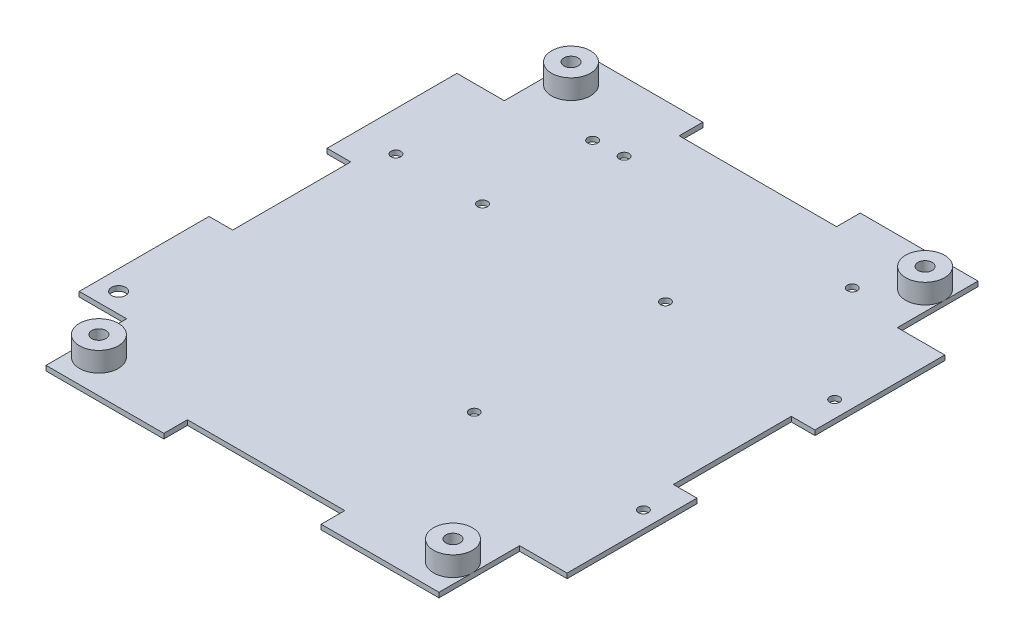
SolidWorks part; units mm, degrees
ref_plane "Front Plane" through (0, 0, 0) normal (0, 0, 1) x (1, 0, 0)
ref_plane "Top Plane" through (0, 0, 0) normal (0, 1, 0) x (1, 0, 0)
ref_plane "Right Plane" through (0, 0, 0) normal (1, 0, 0) x (0, 0, -1)
sketch "Sketch1" plane through (0, 0, 0) normal (0, 1, 0) x (1, 0, 0)
  line L0 (-25.4, 86.995) -> (-63.4314, 86.995)
  line L1 (-88.9, -101.6) -> (88.9, -101.6) construction
  line L2 (101.6, -88.9) -> (101.6, 88.9) construction
  line L3 (88.9, 101.6) -> (-88.9, 101.6) construction
  line L4 (-78.74, -60.96) -> (-63.4314, -60.96)
  line L5 (-63.4314, -60.96) -> (-63.4314, -86.995)
  line L6 (-63.4314, -86.995) -> (-25.4, -86.995)
  line L7 (63.4314, -86.995) -> (63.4314, -60.96)
  line L8 (63.4314, -60.96) -> (78.74, -60.96)
  line L9 (78.74, -60.96) -> (78.74, -25.4)
  line L10 (78.74, 60.96) -> (63.4314, 60.96)
  line L11 (63.4314, 60.96) -> (63.4314, 86.995)
  line L12 (63.4314, 86.995) -> (25.4, 86.995)
  line L13 (-63.4314, 86.995) -> (-63.4314, 60.96)
  line L14 (-63.4314, 60.96) -> (-78.74, 60.96)
  line L15 (-78.74, 60.96) -> (-78.74, 25.4)
  line L16 (-78.74, -25.4) -> (-78.74, -60.96)
  line L17 (-78.74, -25.4) -> (-71.12, -25.4)
  line L19 (-78.74, 25.4) -> (-71.12, 25.4)
  line L20 (-71.12, -25.4) -> (-71.12, 25.4)
  line L22 (-25.4, 86.995) -> (-25.4, 79.375)
  line L23 (-25.4, 79.375) -> (25.4, 79.375)
  line L24 (25.4, 86.995) -> (25.4, 79.375)
  line L25 (78.74, 25.4) -> (71.12, 25.4)
  line L27 (78.74, -25.4) -> (71.12, -25.4)
  line L28 (71.12, 25.4) -> (71.12, -25.4)
  line L30 (25.4, -86.995) -> (25.4, -79.375)
  line L31 (25.4, -79.375) -> (-25.4, -79.375)
  line L32 (-25.4, -86.995) -> (-25.4, -79.375)
  line L33 (78.74, 25.4) -> (78.74, 60.96)
  line L34 (25.4, -86.995) -> (63.4314, -86.995)
  line L35 (-101.6, 88.9) -> (-101.6, -88.9) construction
  arc A0 (88.9, -101.6) -> (101.6, -88.9) centre (88.9, -88.9) ccw construction
  arc A1 (-101.6, -88.9) -> (-88.9, -101.6) centre (-88.9, -88.9) ccw construction
  arc A2 (101.6, 88.9) -> (88.9, 101.6) centre (88.9, 88.9) ccw construction
  arc A3 (-101.6, 88.9) -> (-88.9, 101.6) centre (-88.9, 88.9) cw construction
  circle A4 centre (-57.15, 76.2) radius 2.286
  circle A5 centre (57.15, 76.2) radius 2.286
  circle A6 centre (57.15, -76.2) radius 2.286
  circle A7 centre (-57.15, -76.2) radius 2.286
  point P3 (0, 101.6)
  point P5 (101.6, 0)
  point P13 (101.6, 101.6)
  point P16 (-101.6, 101.6)
  point P38 (-71.12, 0)
  point P55 (0, -79.375)
  point P56 (0, 79.375)
  point P57 (71.12, 0)
  dimension "D2" = 12.7
  dimension "D11" = 4.572
  dimension "D8" = 44.45
  dimension "D1" = 203.2
  dimension "D3" = 203.2
  dimension "D4" = 22.86
  dimension "D5" = 15.3086
  dimension "D6" = 35.56
  dimension "D7" = 173.99
  dimension "D12" = 50.8
  dimension "D13" = 25.4
  dimension "D14" = 44.45
  dimension "D15" = 25.4
  dimension "D18" = 7.62
extrude "Main Body" add sketch "Sketch1" along normal blind 1.5875
sketch "Sketch5" plane through (0, 1.5875, 0) normal (0, 1, 0) x (1, 0, 0)
  line L0 (73.406, 30.734) -> (18.796, 30.734)
  line L1 (48.895, 90.17) -> (-32.385, 90.17)
  line L2 (48.895, 90.17) -> (48.895, 39.37)
  line L3 (48.895, 39.37) -> (-32.385, 39.37)
  line L4 (-32.385, 90.17) -> (-32.385, 39.37)
  line L5 (48.895, 90.17) -> (-32.385, 39.37) construction
  line L6 (48.895, 39.37) -> (-32.385, 90.17) construction
  line L7 (45.085, 64.77) -> (-28.575, 64.77)
  line L8 (-60.96, -54.61) -> (-15.24, -54.61)
  line L9 (-60.96, -54.61) -> (-60.96, 11.43)
  line L10 (-60.96, 11.43) -> (-15.24, 11.43)
  line L11 (-15.24, -54.61) -> (-15.24, 11.43)
  line L13 (-35.56, 26.035) -> (-68.58, 26.035)
  line L14 (-35.56, 26.035) -> (-35.56, 66.675)
  line L15 (-35.56, 66.675) -> (-68.58, 66.675)
  line L16 (-68.58, 26.035) -> (-68.58, 66.675)
  line L17 (-35.56, 26.035) -> (-68.58, 66.675) construction
  line L18 (-35.56, 66.675) -> (-68.58, 26.035) construction
  line L19 (-38.1, 28.575) -> (-66.04, 28.575)
  line L20 (-38.1, 28.575) -> (-38.1, 64.135)
  line L21 (-38.1, 64.135) -> (-66.04, 64.135)
  line L22 (-66.04, 28.575) -> (-66.04, 64.135)
  line L23 (-38.1, 28.575) -> (-66.04, 64.135) construction
  line L24 (-38.1, 64.135) -> (-66.04, 28.575) construction
  line L26 (73.406, -30.988) -> (18.796, -30.988)
  line L28 (73.406, -30.988) -> (73.406, 30.734)
  line L30 (73.406, 30.734) -> (18.796, 30.734)
  line L31 (18.796, -30.988) -> (18.796, 30.734)
  line L32 (73.406, -30.988) -> (18.796, 30.734) construction
  line L33 (73.406, 30.734) -> (18.796, -30.988) construction
  line L36 (25.4, 86.995) -> (25.4, 79.375)
  line L38 (25.4, 79.375) -> (-25.4, 79.375)
  line L40 (71.12, 25.4) -> (78.74, 25.4)
  line L41 (78.74, 25.4) -> (78.74, 60.96)
  line L42 (78.74, 60.96) -> (63.4314, 60.96)
  line L43 (63.4314, 60.96) -> (63.4314, 86.995)
  line L44 (63.4314, 86.995) -> (25.4, 86.995)
  line L45 (25.4, 79.375) -> (-25.4, 79.375)
  line L49 (-63.4314, 86.995) -> (-63.4314, 60.96)
  line L50 (-63.4314, 60.96) -> (-78.74, 60.96)
  line L51 (-78.74, 60.96) -> (-78.74, 25.4)
  line L52 (-78.74, 25.4) -> (-71.12, 25.4)
  line L53 (-71.12, 25.4) -> (-71.12, -25.4)
  line L54 (-71.12, -25.4) -> (-78.74, -25.4)
  line L55 (-78.74, -25.4) -> (-78.74, -60.96)
  line L56 (-78.74, -60.96) -> (-63.4314, -60.96)
  line L57 (-63.4314, -60.96) -> (-63.4314, -86.995)
  line L58 (-63.4314, -86.995) -> (-25.4, -86.995)
  line L61 (71.12, -25.4) -> (71.12, 25.4)
  line L62 (71.12, -25.4) -> (71.12, 25.4)
  line L63 (63.4314, -86.995) -> (63.4314, -60.96)
  line L64 (63.4314, -60.96) -> (78.74, -60.96)
  line L65 (78.74, -60.96) -> (78.74, -25.4)
  line L66 (78.74, -25.4) -> (71.12, -25.4)
  line L74 (71.12, 25.4) -> (78.74, 25.4)
  line L75 (78.74, 25.4) -> (78.74, 60.96)
  line L76 (78.74, 60.96) -> (63.4314, 60.96)
  line L77 (63.4314, 60.96) -> (63.4314, 86.995)
  line L78 (63.4314, 86.995) -> (25.4, 86.995)
  line L83 (-63.4314, 86.995) -> (-63.4314, 60.96)
  line L84 (-63.4314, 60.96) -> (-78.74, 60.96)
  line L85 (-78.74, 60.96) -> (-78.74, 25.4)
  line L86 (-78.74, 25.4) -> (-71.12, 25.4)
  line L87 (-71.12, 25.4) -> (-71.12, -25.4)
  line L88 (-71.12, -25.4) -> (-78.74, -25.4)
  line L89 (-78.74, -25.4) -> (-78.74, -60.96)
  line L90 (-78.74, -60.96) -> (-63.4314, -60.96)
  line L91 (-63.4314, -60.96) -> (-63.4314, -86.995)
  line L92 (-63.4314, -86.995) -> (-25.4, -86.995)
  line L97 (63.4314, -86.995) -> (63.4314, -60.96)
  line L98 (63.4314, -60.96) -> (78.74, -60.96)
  line L99 (78.74, -60.96) -> (78.74, -25.4)
  line L100 (78.74, -25.4) -> (71.12, -25.4)
  line L107 (-25.4, 86.995) -> (-63.4314, 86.995)
  line L109 (-25.4, 86.995) -> (-63.4314, 86.995)
  line L110 (-25.4, -86.995) -> (-25.4, -79.375)
  line L111 (-25.4, -86.995) -> (-25.4, -79.375)
  line L112 (-25.4, -79.375) -> (25.4, -79.375)
  line L113 (-25.4, -79.375) -> (25.4, -79.375)
  line L114 (25.4, -79.375) -> (25.4, -86.995)
  line L115 (25.4, -79.375) -> (25.4, -86.995)
  line L116 (25.4, -86.995) -> (63.4314, -86.995)
  line L117 (25.4, -86.995) -> (63.4314, -86.995)
  line L122 (25.4, 86.995) -> (25.4, 79.375)
  line L126 (-25.4, 79.375) -> (-25.4, 86.995)
  line L127 (-25.4, 79.375) -> (-25.4, 86.995)
  circle A0 centre (18.796, 30.734) radius 1.5875
  circle A1 centre (73.406, 30.734) radius 1.5875
  circle A2 centre (73.406, -30.988) radius 1.5875
  circle A3 centre (18.796, -30.988) radius 1.5875
  circle A4 centre (-15.24, -54.61) radius 1.27
  circle A5 centre (-60.96, -54.61) radius 1.27
  circle A6 centre (-60.96, 11.43) radius 1.27
  circle A7 centre (-15.24, 11.43) radius 1.27
  circle A8 centre (-28.575, 64.77) radius 1.5875
  circle A9 centre (45.085, 64.77) radius 1.5875
  circle A10 centre (-66.04, 28.575) radius 1.5875
  circle A11 centre (-66.04, 64.135) radius 1.5875
  circle A12 centre (-38.1, 64.135) radius 1.5875
  circle A13 centre (-38.1, 28.575) radius 1.5875
  circle A14 centre (57.15, 76.2) radius 2.286 construction
  circle A15 centre (-57.15, 76.2) radius 2.286 construction
  circle A16 centre (57.15, 76.2) radius 2.286
  circle A17 centre (-57.15, 76.2) radius 2.286
  circle A18 centre (57.15, 76.2) radius 6.2814
  circle A19 centre (-57.15, 76.2) radius 6.2814
  circle A20 centre (-72.39, -54.61) radius 2.286
  text T0 "<b>LIPO</b>"
  point P0 (8.255, 64.77)
  point P2 (73.406, -30.988)
  point P4 (18.796, -30.988)
  point P6 (18.796, 30.734)
  point P8 (73.406, 30.734)
  point P25 (46.101, 30.734)
  point P40 (-15.24, -21.59)
  point P42 (-38.1, 11.43)
  point P44 (-38.1, -21.59)
  point P52 (-52.07, 46.355)
  point P57 (-52.07, 46.355)
  point P58 (8.255, 64.77)
  point P78 (-52.07, 66.675)
  point P81 (46.101, -0.127)
  dimension "D8" = 3.175
  dimension "D9" = 3.175
  dimension "D10" = 3.175
  dimension "D11" = 3.175
  dimension "D17" = 2.54
  dimension "D20" = 3.175
  dimension "D27" = 3.175
  dimension "D30" = 4.572
  dimension "D33" = 5.334
  dimension "D14" = 5.334
  dimension "D2" = 54.61
  dimension "D4" = 81.28
  dimension "D5" = 61.722
  dimension "D6" = 50.8
  dimension "D7" = 22.225
  dimension "D12" = 21.59
  dimension "D13" = 28.575
  dimension "D15" = 45.72
  dimension "D16" = 66.04
  dimension "D18" = 21.59
  dimension "D19" = 38.1
  dimension "D21" = 73.66
  dimension "D22" = 3.175
  dimension "D23" = 40.64
  dimension "D24" = 33.02
  dimension "D25" = 35.56
  dimension "D26" = 27.94
  dimension "D28" = 3.175
  dimension "D29" = 9.525
  dimension "D31" = 6.35
  dimension "D32" = 6.35
  dimension "D1" = 0
sketch "Sketch13" plane through (0, 1.5875, 0) normal (0, 1, 0) x (1, 0, 0)
  line L32 (25.4, 79.375) -> (-25.4, 79.375)
  line L33 (25.4, 86.995) -> (25.4, 79.375)
  line L36 (63.4314, 86.995) -> (25.4, 86.995)
  line L37 (-63.4314, 86.995) -> (-63.4314, 60.96)
  line L38 (-63.4314, 60.96) -> (-78.74, 60.96)
  line L39 (-78.74, 60.96) -> (-78.74, 25.4)
  line L40 (-78.74, 25.4) -> (-71.12, 25.4)
  line L41 (-71.12, 25.4) -> (-71.12, -25.4)
  line L42 (-71.12, -25.4) -> (-78.74, -25.4)
  line L43 (-78.74, -25.4) -> (-78.74, -60.96)
  line L44 (-78.74, -60.96) -> (-63.4314, -60.96)
  line L45 (-63.4314, -60.96) -> (-63.4314, -86.995)
  line L46 (-63.4314, -86.995) -> (-25.4, -86.995)
  line L47 (-25.4, -86.995) -> (-25.4, -79.375)
  line L48 (-25.4, -79.375) -> (25.4, -79.375)
  line L49 (25.4, -79.375) -> (25.4, -86.995)
  line L50 (25.4, -86.995) -> (63.4314, -86.995)
  line L51 (63.4314, -86.995) -> (63.4314, -60.96)
  line L52 (63.4314, -60.96) -> (78.74, -60.96)
  line L53 (78.74, -60.96) -> (78.74, -25.4)
  line L54 (78.74, -25.4) -> (71.12, -25.4)
  line L55 (71.12, -25.4) -> (71.12, 25.4)
  line L56 (71.12, 25.4) -> (78.74, 25.4)
  line L57 (78.74, 25.4) -> (78.74, 60.96)
  line L58 (78.74, 60.96) -> (63.4314, 60.96)
  line L59 (63.4314, 60.96) -> (63.4314, 86.995)
  line L60 (-25.4, 86.995) -> (-63.4314, 86.995)
  line L61 (25.4, 86.995) -> (25.4, 79.375)
  line L64 (25.4, 79.375) -> (-25.4, 79.375)
  line L68 (63.4314, 86.995) -> (25.4, 86.995)
  line L69 (-63.4314, 86.995) -> (-63.4314, 60.96)
  line L70 (-63.4314, 60.96) -> (-78.74, 60.96)
  line L71 (-78.74, 60.96) -> (-78.74, 25.4)
  line L72 (-78.74, 25.4) -> (-71.12, 25.4)
  line L73 (-71.12, 25.4) -> (-71.12, -25.4)
  line L74 (-71.12, -25.4) -> (-78.74, -25.4)
  line L75 (-78.74, -25.4) -> (-78.74, -60.96)
  line L76 (-78.74, -60.96) -> (-63.4314, -60.96)
  line L77 (-63.4314, -60.96) -> (-63.4314, -86.995)
  line L78 (-63.4314, -86.995) -> (-25.4, -86.995)
  line L79 (-25.4, -86.995) -> (-25.4, -79.375)
  line L80 (-25.4, -79.375) -> (25.4, -79.375)
  line L81 (25.4, -79.375) -> (25.4, -86.995)
  line L82 (25.4, -86.995) -> (63.4314, -86.995)
  line L83 (63.4314, -86.995) -> (63.4314, -60.96)
  line L84 (63.4314, -60.96) -> (78.74, -60.96)
  line L85 (78.74, -60.96) -> (78.74, -25.4)
  line L86 (78.74, -25.4) -> (71.12, -25.4)
  line L87 (71.12, -25.4) -> (71.12, 25.4)
  line L88 (71.12, 25.4) -> (78.74, 25.4)
  line L89 (78.74, 25.4) -> (78.74, 60.96)
  line L90 (78.74, 60.96) -> (63.4314, 60.96)
  line L91 (63.4314, 60.96) -> (63.4314, 86.995)
  line L104 (-25.4, 79.375) -> (-25.4, 86.995)
  line L105 (-25.4, 79.375) -> (-25.4, 86.995)
  line L108 (-25.4, 86.995) -> (-63.4314, 86.995)
  circle A0 centre (57.15, 76.2) radius 2.286 construction
  circle A1 centre (-57.15, 76.2) radius 2.286 construction
  circle A2 centre (-57.15, -76.2) radius 2.286 construction
  circle A3 centre (57.15, -76.2) radius 2.286 construction
  circle A4 centre (57.15, 76.2) radius 2.286
  circle A5 centre (-57.15, 76.2) radius 2.286
  circle A6 centre (-57.15, -76.2) radius 2.286
  circle A7 centre (57.15, -76.2) radius 2.286
  circle A8 centre (57.15, 76.2) radius 6.2814
  circle A9 centre (-57.15, -76.2) radius 6.2814
  circle A10 centre (-57.15, 76.2) radius 6.2814
  circle A11 centre (57.15, -76.2) radius 6.2814
  point P40 (-57.15, -76.2)
  point P46 (57.15, 76.2)
  point P52 (57.15, -76.2)
  point P58 (-57.15, 76.2)
  dimension "D1" = 0
extrude "Boss-Extrude9" add sketch "Sketch13" along normal blind 6.35
extrude "Cut-Extrude3" cut sketch "Sketch5" against normal up to next contours A2 | A3 | A0 | A1 | A13 | A10 | A12 | A8 | A9 | A20
sketch "Sketch14" plane through (0, 1.5875, 0) normal (0, 1, 0) x (1, 0, 0)
  line L28 (71.12, -25.4) -> (71.12, 25.4) construction
  line L29 (71.12, 25.4) -> (78.74, 25.4) construction
  line L30 (78.74, 25.4) -> (78.74, 60.96) construction
  line L32 (78.74, 25.4) -> (78.74, 60.96)
  line L33 (71.12, 25.4) -> (78.74, 25.4)
  line L34 (71.12, -25.4) -> (71.12, 25.4)
  line L35 (78.74, 25.4) -> (78.74, 19.05)
  line L36 (78.74, 19.05) -> (71.12, 19.05)
  line L37 (78.74, -60.96) -> (78.74, -25.4) construction
  line L38 (78.74, -25.4) -> (71.12, -25.4) construction
  line L39 (78.74, -60.96) -> (78.74, -25.4)
  line L40 (78.74, -25.4) -> (71.12, -25.4)
  line L41 (78.74, -25.4) -> (78.74, -19.05)
  line L42 (78.74, -19.05) -> (71.12, -19.05)
  line L43 (0, 0) -> (0, 23.2072) construction
  line L44 (-78.74, 25.4) -> (-78.74, 19.05)
  line L45 (-78.74, 19.05) -> (-71.12, 19.05)
  line L46 (-78.74, -19.05) -> (-71.12, -19.05)
  line L47 (-78.74, -25.4) -> (-78.74, -19.05)
  line L48 (-78.74, 25.4) -> (-71.12, 25.4) construction
  line L49 (-71.12, 25.4) -> (-71.12, -25.4) construction
  line L50 (-71.12, -25.4) -> (-78.74, -25.4) construction
  line L51 (-78.74, 25.4) -> (-71.12, 25.4)
  line L52 (-71.12, 25.4) -> (-71.12, -25.4)
  line L53 (-71.12, -25.4) -> (-78.74, -25.4)
  line M29 (-78.74, 25.4) -> (-71.12, 25.4)
  line M30 (-71.12, 25.4) -> (-71.12, -25.4)
  line M31 (-71.12, -25.4) -> (-78.74, -25.4)
  line M47 (78.74, -25.4) -> (71.12, -25.4)
  line M48 (71.12, -25.4) -> (71.12, 25.4)
  line M49 (71.12, 25.4) -> (78.74, 25.4)
  dimension "D1" = 6.35
extrude "Boss-Extrude10" add sketch "Sketch14" against normal up to surface (1.5875 mm away) contours L47 L46 M31 M30 | L44 L45 M30 M29 | L41 L42 M48 M47 | L36 L35 L34 M49 up to face at (-72.39, 0, 56.896)
